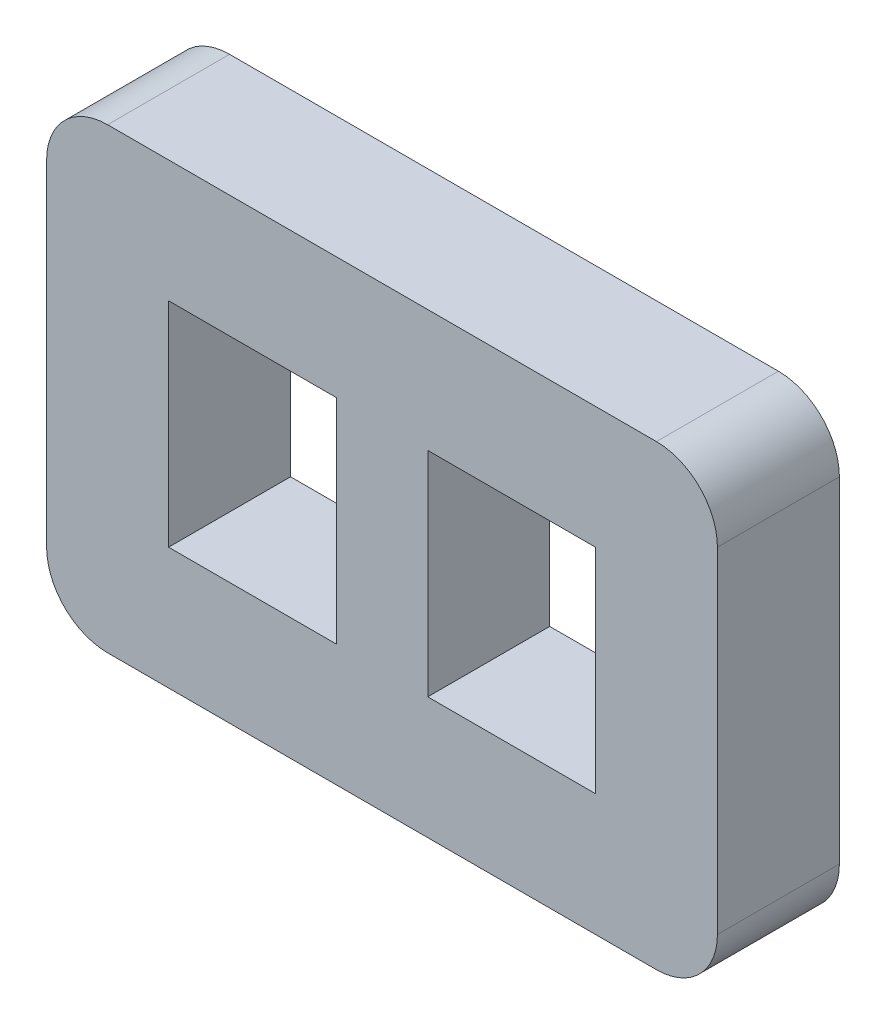
SolidWorks part; units mm, degrees
ref_plane "Front Plane" through (0, 0, 0) normal (0, 0, 1) x (1, 0, 0)
ref_plane "Top Plane" through (0, 0, 0) normal (0, 1, 0) x (1, 0, 0)
ref_plane "Right Plane" through (0, 0, 0) normal (1, 0, 0) x (0, 0, -1)
sketch "Sketch1" plane through (0, 0, 0) normal (0, 0, 1) x (1, 0, 0)
  line L0 (0, 19) -> (0, 14.0065) construction
  line L2 (-3, 17.75) -> (3, 17.75) construction
  line L5 (4.5, 21.5) -> (-4.5, 21.5)
  line L6 (3.5, 16) -> (0.75, 16)
  line L7 (3.5, 16) -> (3.5, 19.5)
  line L8 (3.5, 19.5) -> (0.75, 19.5)
  line L9 (-3.5, 16) -> (-3.5, 19.5)
  line L10 (3.5, 16) -> (-3.5, 19.5) construction
  line L11 (3.5, 19.5) -> (-3.5, 16) construction
  line L12 (-5.5, 15) -> (-5.5, 20.5)
  line L13 (4.5, 14) -> (-4.5, 14)
  line L14 (5.5, 15) -> (5.5, 20.5)
  line L15 (-0.75, 19.5) -> (-3.5, 19.5)
  line L16 (-5.5, 14) -> (-5.5, 21.5) construction
  line L17 (0.75, 16) -> (0.75, 19.5)
  line L18 (-0.75, 16) -> (-3.5, 16)
  line L19 (-0.75, 16) -> (-0.75, 19.5)
  line L20 (0.75, 16) -> (-0.75, 19.5) construction
  line L21 (0.75, 19.5) -> (-0.75, 16) construction
  line L22 (3.5, 19.5) -> (-3.5, 19.5) construction
  line L23 (3.5, 16) -> (-3.5, 16) construction
  line L24 (5.5, 14) -> (-5.5, 14) construction
  line L25 (5.5, 14) -> (5.5, 21.5) construction
  line L26 (5.5, 21.5) -> (-5.5, 21.5) construction
  arc A0 (-5.5, 15) -> (-4.5, 14) centre (-4.5, 15) ccw
  arc A1 (4.5, 14) -> (5.5, 15) centre (4.5, 15) ccw
  arc A2 (5.5, 20.5) -> (4.5, 21.5) centre (4.5, 20.5) ccw
  arc A3 (-5.5, 20.5) -> (-4.5, 21.5) centre (-4.5, 20.5) cw
  point P11 (0, 17.75)
  point P20 (0, 17.75)
  dimension "D5" = 1
  dimension "D1" = 3.5
  dimension "D2" = 7
  dimension "D4" = 1.5
  dimension "D3" = 2
extrude "Boss-Extrude1" add sketch "Sketch1" along normal blind 2
